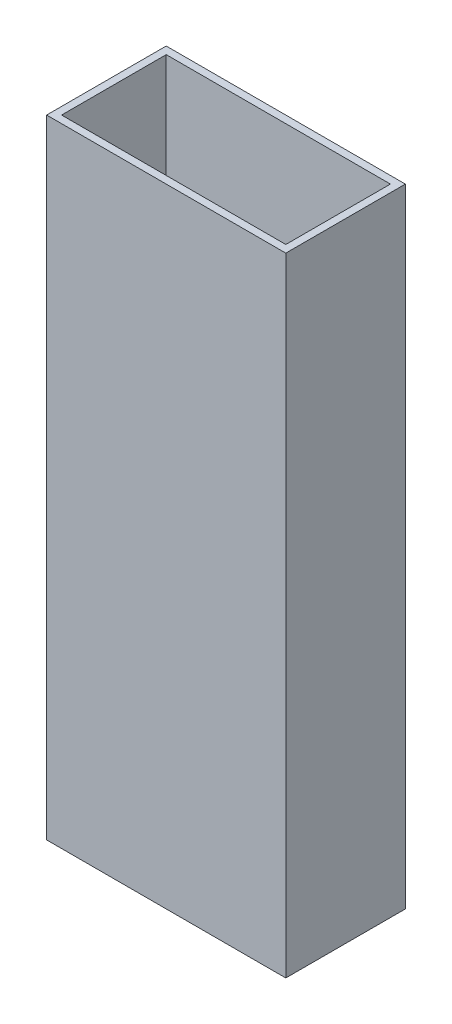
SolidWorks part; units mm, degrees
ref_plane "Front Plane" through (0, 0, 0) normal (0, 0, 1) x (1, 0, 0)
ref_plane "Top Plane" through (0, 0, 0) normal (0, 1, 0) x (1, 0, 0)
ref_plane "Right Plane" through (0, 0, 0) normal (1, 0, 0) x (0, 0, -1)
sketch "Sketch1" plane through (0, 0, 0) normal (0, 1, 0) x (1, 0, 0)
  line L1 (-18.4198, 12.5061) -> (32.3802, 12.5061)
  line L2 (-18.4198, 12.5061) -> (-18.4198, -12.8939)
  line L3 (-18.4198, -12.8939) -> (32.3802, -12.8939)
  line L4 (32.3802, 12.5061) -> (32.3802, -12.8939)
  line L5 (-16.8323, 10.9186) -> (30.7927, 10.9186)
  line L6 (-16.8323, 10.9186) -> (-16.8323, -11.3064)
  line L7 (-16.8323, -11.3064) -> (30.7927, -11.3064)
  line L8 (30.7927, 10.9186) -> (30.7927, -11.3064)
  dimension "D1" = 50.8
  dimension "D2" = 25.4
  dimension "D3" = 1.5875
  dimension "D4" = 1.5875
  dimension "D5" = 1.5875
  dimension "D6" = 1.5875
extrude "Boss-Extrude1" add sketch "Sketch1" along normal blind 133.35
